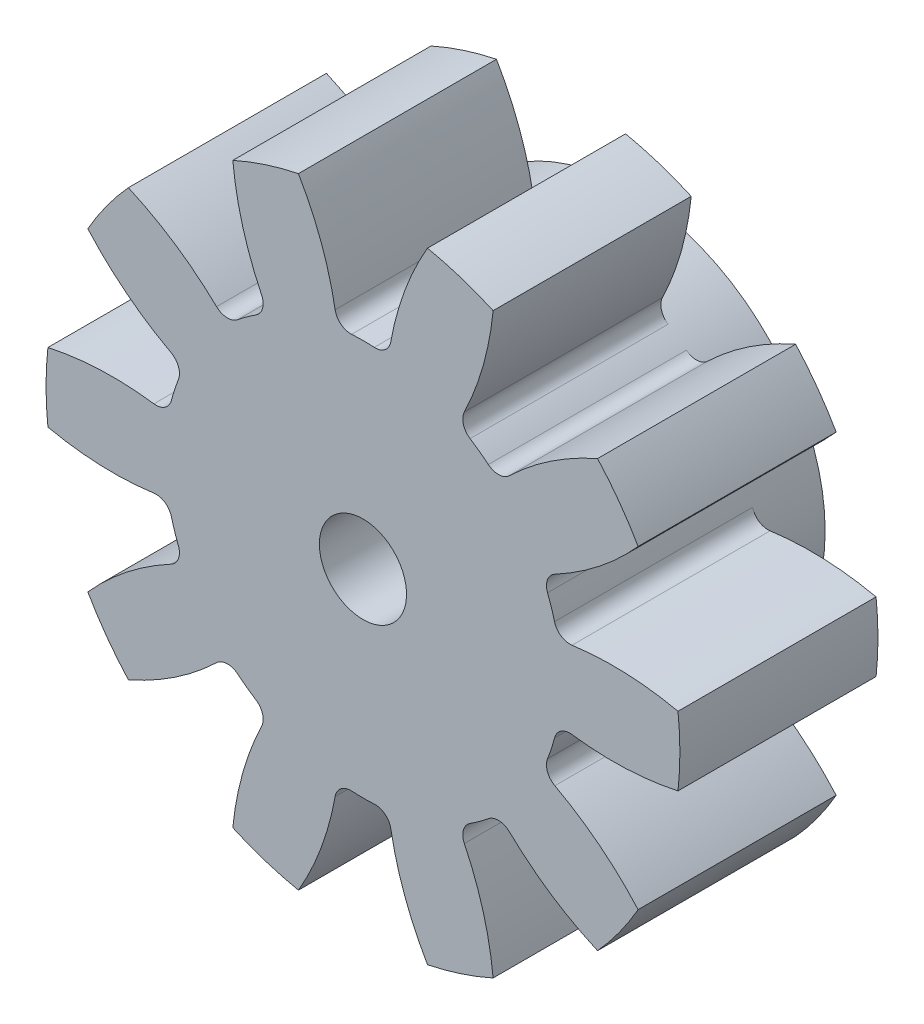
SolidWorks part; units mm, degrees
ref_plane "Front Plane" through (0, 0, 0) normal (0, 0, 1) x (1, 0, 0)
ref_plane "Top Plane" through (0, 0, 0) normal (0, 1, 0) x (1, 0, 0)
ref_plane "Right Plane" through (0, 0, 0) normal (1, 0, 0) x (0, 0, -1)
sketch "Sketch1" plane through (0, 0, 0) normal (0, 0, 1) x (1, 0, 0)
  circle A0 centre (0, 0) radius 10
  circle A1 centre (0, 0) radius 12
  circle A2 centre (0, 0) radius 7.5
  dimension "D1" = 20
  dimension "D2" = 24
  dimension "D3" = 4.5
extrude "Boss-Extrude1" add sketch "Sketch1" along normal mid plane 425 contours A1
sketch "Sketch2" plane through (0, 0, 0) normal (0, 0, 1) x (1, 0, 0)
  line L0 (0, 0) -> (0, 12) construction
  line L1 (-1.5643, 9.8769) -> (1.5643, 9.8769) construction
  line L2 (-0.9691, 7.4371) -> (0, 0) construction
  line L3 (0, 5.5789) -> (-2.6051, 12.7363) construction
  line L4 (0, 0) -> (3.7082, 11.4127) construction
  line L5 (1.5643, 9.8769) -> (4.5399, 8.9101) construction
  circle A0 centre (0, 0) radius 12 construction
  arc A1 (-3.0254, 12.6431) -> (-0.9691, 7.4371) centre (-12.3373, 5.9558) cw
  arc A2 (3.0254, 12.6431) -> (0.9691, 7.4371) centre (12.3373, 5.9558) ccw
  circle A3 centre (0, 0) radius 7.5 construction
  arc A4 (0.9691, 7.4371) -> (-0.9691, 7.4371) centre (0, 0) ccw
  circle A5 centre (0, 0) radius 12 construction
  circle A6 centre (0, 0) radius 10 construction
  circle A7 centre (0, 0) radius 13
  arc A8 (3.0254, 12.6431) -> (-3.0254, 12.6431) centre (0, 0) ccw
  dimension "D2" = 1.9081
  dimension "D3" = 20
  dimension "D4" = 18
  dimension "D1" = 1
extrude "Cut-Extrude1" cut sketch "Sketch2" against normal through all both and the other way through all
fillet "Fillet1" radius 0.6 1 edges at (-0.9691, 7.4371, 0)
fillet "Fillet2" radius 0.6 1 edges at (0.9691, 7.4371, 0)
sketch "Sketch3" plane through (0, 0, -212.5) normal (0, 0, -1) x (-1, 0, 0)
pattern_circular "CirPattern2" count 10 over 360 about axis through (0, 0, 0) along (0, 0, 1) of "Cut-Extrude1", "Fillet1", "Fillet2"
sketch "Sketch4" plane through (0, 0, -212.5) normal (0, 0, -1) x (-1, 0, 0)
  circle A0 centre (0, 0) radius 7.5
  circle A1 centre (0, 0) radius 3
  dimension "D1" = 6
extrude "Boss-Extrude2" add sketch "Sketch4" along normal mid plane 5 contours A0 | A1
sketch "Sketch5" plane through (0, 0, -212.5) normal (0, 0, -1) x (-1, 0, 0)
  circle A0 centre (0, 0) radius 3
extrude "Cut-Extrude2" cut sketch "Sketch5" against normal blind 32 and the other way through all
sketch "Sketch6" plane through (0, 0, 212.5) normal (0, 0, 1) x (1, 0, 0)
  circle A0 centre (0, 0) radius 7.5
  dimension "D1" = 15
extrude "Boss-Extrude3" add sketch "Sketch6" along normal mid plane 12
ref_plane "Plane1" through (0, 0, -205) normal (0, 0, -1) x (-1, 0, 0)
sketch "Sketch7" plane through (0, 0, 218.5) normal (0, 0, 1) x (1, 0, 0)
  circle A0 centre (0, 0) radius 12
extrude "Cut-Extrude3" cut sketch "Sketch7" against normal up to surface (423.5 mm away) contours A0
sketch "Sketch8" plane through (0, 0, -215) normal (0, 0, -1) x (-1, 0, 0)
  circle A0 centre (0, 0) radius 1.65
  circle A1 centre (0, 0) radius 7.5
  dimension "D1" = 3.3
extrude "Boss-Extrude4" add sketch "Sketch8" against normal up to surface (10 mm away) up to face at (-3, 0, -205)
equation "\"Module\"= 2mm"
equation "\"Number of Teeth\"= 10"
equation "\"D1@Sketch1\"=\"Module\" * \"Number of Teeth\""
equation "\"D2@Sketch1\"=(\"Number of Teeth\" + 2) * \"Module\""
equation "\"D3@Sketch1\"=\"Module\" * if( \"Module\" = > 1.25, 2.25, 2.4)"
equation "\"D4@Sketch2\"=180 / \"Number of Teeth\""
equation "\"D1@Fillet1\"=0.3 * \"Module\""
